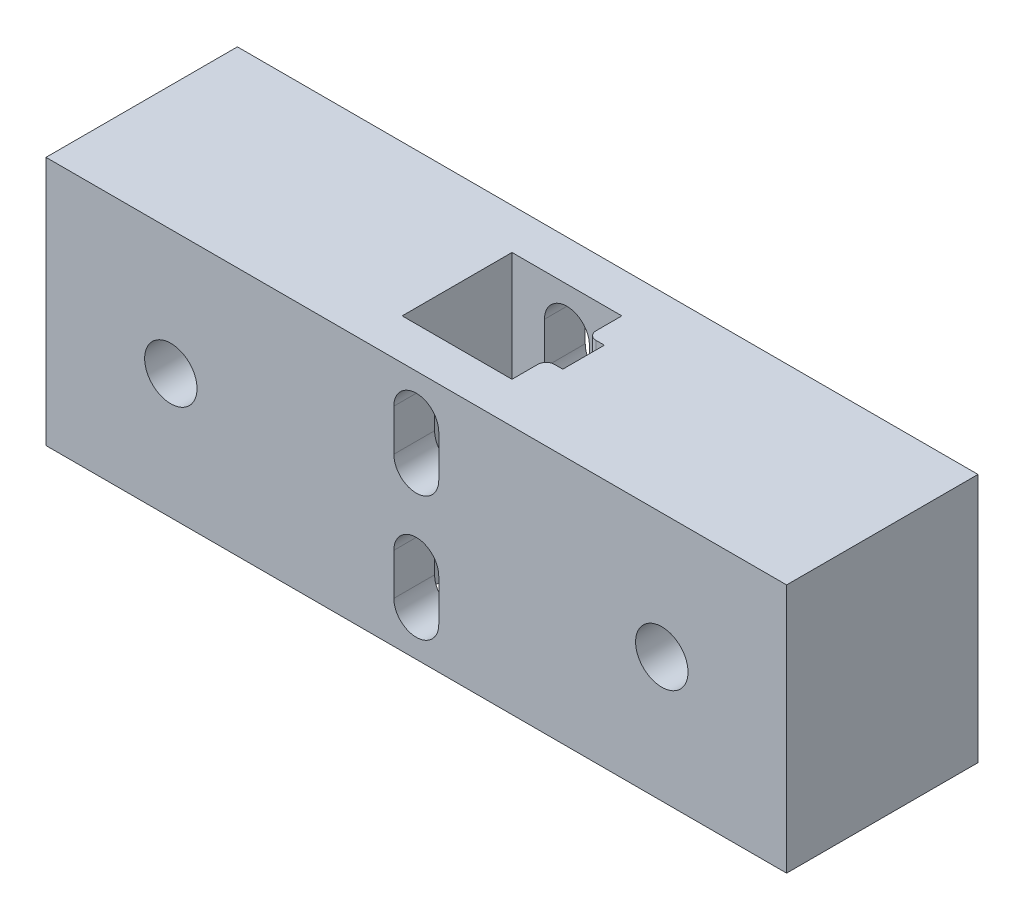
SolidWorks part; units mm, degrees
ref_plane "Plan de face" through (0, 0, 0) normal (0, 0, 1) x (1, 0, 0)
ref_plane "Plan de dessus" through (0, 0, 0) normal (0, 1, 0) x (1, 0, 0)
ref_plane "Plan de droite" through (0, 0, 0) normal (1, 0, 0) x (0, 0, -1)
sketch "Esquisse1" plane through (0, 0, 0) normal (0, 0, 1) x (1, 0, 0)
  line L1 (-4.11, 1.9089) -> (84.89, 1.9089)
  line L2 (-4.11, 1.9089) -> (-4.11, -28.0911)
  line L3 (-4.11, -28.0911) -> (84.89, -28.0911)
  line L4 (84.89, 1.9089) -> (84.89, -28.0911)
  dimension "D1" = 89
  dimension "D2" = 30
extrude "Boss.-Extru.1" add sketch "Esquisse1" along normal blind 23
sketch "Esquisse2" plane through (0, 1.9089, 0) normal (0, 1, 0) x (1, 0, 0)
  line L0 (40.39, -23) -> (40.39, 0) construction
  line L1 (40.39, -11.5) -> (48.99, -11.5) construction
  line L2 (46.99, -4.9) -> (33.79, -4.9)
  line L3 (46.99, -4.9) -> (46.99, -18.1)
  line L4 (84.89, 0) -> (-4.11, 0)
  line L5 (-4.11, 0) -> (-4.11, -23)
  line L6 (-4.11, -23) -> (84.89, -23)
  line L7 (84.89, -23) -> (84.89, 0)
  line L8 (84.89, 0) -> (-4.11, 0)
  line L9 (-4.11, 0) -> (-4.11, -23)
  line L10 (-4.11, -23) -> (84.89, -23)
  line L11 (84.89, -23) -> (84.89, 0)
  line L12 (46.99, -18.1) -> (33.79, -18.1)
  line L13 (33.79, -4.9) -> (33.79, -18.1)
  line L14 (46.99, -4.9) -> (33.79, -18.1) construction
  line L15 (46.99, -18.1) -> (33.79, -4.9) construction
  line L16 (46.99, -14) -> (48.99, -14)
  line L17 (46.99, -14) -> (46.99, -9)
  line L18 (46.99, -9) -> (48.99, -9)
  line L19 (48.99, -14) -> (48.99, -9)
  point P6 (40.39, -11.5)
  point P7 (40.39, -11.5)
  dimension "D2" = 13.2
  dimension "D3" = 13.2
  dimension "D4" = 2
  dimension "D5" = 5
  dimension "D1" = 0
extrude "Enlèv. mat.-Extru.1" cut sketch "Esquisse2" against normal through all contours L2 L13 L12 L3 | L16 L19 L18 L3
sketch "Esquisse3" plane through (0, 0, 0) normal (0, 0, -1) x (-1, 0, 0)
  line L0 (-40.39, -28.0911) -> (-40.39, 1.9089) construction
  line L1 (4.11, -13.0911) -> (-84.89, -13.0911) construction
  line L4 (4.11, -28.0911) -> (4.11, 1.9089)
  line L5 (4.11, 1.9089) -> (-84.89, 1.9089)
  line L6 (-84.89, 1.9089) -> (-84.89, -28.0911)
  line L7 (-84.89, -28.0911) -> (4.11, -28.0911)
  line L8 (4.11, -28.0911) -> (4.11, 1.9089)
  line L9 (4.11, 1.9089) -> (-84.89, 1.9089)
  line L10 (-84.89, 1.9089) -> (-84.89, -28.0911)
  line L11 (-84.89, -28.0911) -> (4.11, -28.0911)
  circle A0 centre (-10.89, -13.0911) radius 3.15
  circle A1 centre (-69.89, -13.0911) radius 3.15
  point P8 (-10.89, -13.0911)
  dimension "D3" = 6.3
  dimension "D2" = 15
  dimension "D1" = 0
sketch "Esquisse4" plane through (0, 0, 0) normal (0, 0, -1) x (-1, 0, 0)
  line L0 (-40.39, -28.0911) -> (-40.39, 1.9089) construction
  line L1 (-40.39, -23.0911) -> (-40.39, -18.0911) construction
  line L2 (-43.09, -23.0911) -> (-43.09, -18.0911)
  line L3 (-37.69, -23.0911) -> (-37.69, -18.0911)
  line L4 (4.11, -28.0911) -> (4.11, 1.9089)
  line L5 (4.11, 1.9089) -> (-84.89, 1.9089)
  line L6 (-84.89, 1.9089) -> (-84.89, -28.0911)
  line L7 (-84.89, -28.0911) -> (4.11, -28.0911)
  line L8 (4.11, -28.0911) -> (4.11, 1.9089)
  line L9 (4.11, 1.9089) -> (-84.89, 1.9089)
  line L10 (-84.89, 1.9089) -> (-84.89, -28.0911)
  line L11 (-84.89, -28.0911) -> (4.11, -28.0911)
  line L12 (-33.79, 1.9089) -> (-46.99, 1.9089)
  line L13 (-46.99, 1.9089) -> (-46.99, -28.0911)
  line L14 (-46.99, -28.0911) -> (-33.79, -28.0911)
  line L15 (-33.79, -28.0911) -> (-33.79, 1.9089)
  line L16 (-33.79, 1.9089) -> (-46.99, 1.9089)
  line L17 (-46.99, 1.9089) -> (-46.99, -28.0911)
  line L18 (-46.99, -28.0911) -> (-33.79, -28.0911)
  line L19 (-33.79, -28.0911) -> (-33.79, 1.9089)
  line L20 (-46.99, -13.0911) -> (-33.79, -13.0911) construction
  line L21 (-40.39, -3.0911) -> (-40.39, -8.0911) construction
  line L22 (-43.09, -3.0911) -> (-43.09, -8.0911)
  line L23 (-37.69, -3.0911) -> (-37.69, -8.0911)
  arc A2 (-43.09, -23.0911) -> (-37.69, -23.0911) centre (-40.39, -23.0911) ccw
  arc A3 (-37.69, -18.0911) -> (-43.09, -18.0911) centre (-40.39, -18.0911) ccw
  arc A4 (-43.09, -3.0911) -> (-37.69, -3.0911) centre (-40.39, -3.0911) cw
  arc A5 (-37.69, -8.0911) -> (-43.09, -8.0911) centre (-40.39, -8.0911) cw
  point P12 (-40.39, -20.5911)
  point P21 (-40.39, -5.5911)
  dimension "D3" = 2.7
  dimension "D4" = 5
  dimension "D5" = 5
  dimension "D1" = 0
  dimension "D2" = 0
extrude "Enlèv. mat.-Extru.2" cut sketch "Esquisse3" against normal through all contours A0 | A1
extrude "Enlèv. mat.-Extru.3" cut sketch "Esquisse4" against normal through all contours A5 L23 A4 L22 | L2 A3 L3 A2
fillet "Congé1" radius 1 2 edges at (46.99, -13.0911, 9) (46.99, -13.0911, 14)
